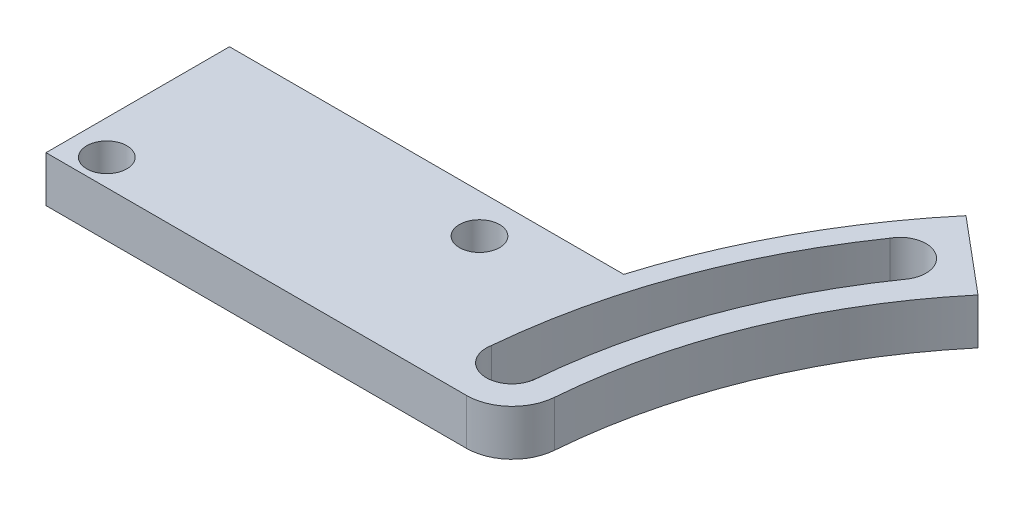
SolidWorks part; units mm, degrees
ref_plane "Front Plane" through (0, 0, 0) normal (0, 0, 1) x (1, 0, 0)
ref_plane "Top Plane" through (0, 0, 0) normal (0, 1, 0) x (1, 0, 0)
ref_plane "Right Plane" through (0, 0, 0) normal (1, 0, 0) x (0, 0, -1)
sketch "Sketch1" plane through (0, 0, 0) normal (0, 1, 0) x (1, 0, 0)
  circle A0 centre (0, 0) radius 55
  dimension "D1" = 110
extrude "Boss-Extrude1" add sketch "Sketch1" along normal blind 4
sketch "Sketch6" plane through (0, 0, 0) normal (0, 1, 0) x (1, 0, 0)
  line L0 (0, 0) -> (-87, 0) construction
  line L1 (-87, 0) -> (0, 0)
  line L2 (-87, 0) -> (-87, 16)
  line L3 (0, 0) -> (0, 16)
  line L4 (-87, 16) -> (0, 16)
  dimension "D1" = 16
  dimension "D2" = 87
extrude "Boss-Extrude2" add sketch "Sketch6" along normal blind 4
sketch "Sketch2" plane through (0, 0, 0) normal (0, 1, 0) x (1, 0, 0)
  circle A0 centre (0, 0) radius 46.5
  dimension "D1" = 93
extrude "Cut-Extrude1" cut sketch "Sketch2" along normal through all
sketch "Sketch3" plane through (0, 0, 0) normal (0, 1, 0) x (1, 0, 0)
  line L0 (0, 0) -> (-51, 0) construction
  line L1 (0, 0) -> (-50.8059, 4.4449) construction
  circle A0 centre (0, 0) radius 51 construction
  circle A1 centre (-50.8059, 4.4449) radius 2.25
  dimension "D1" = 4.5
  dimension "D3" = 102
  dimension "D2" = 5
extrude "Cut-Extrude2" cut sketch "Sketch3" along normal through all
pattern_circular "CirPattern1" count 12 over 360 about axis through (0, 0, 0) along (0, 1, 0) of "Cut-Extrude2"
sketch "Sketch4" plane through (0, 0, 0) normal (0, 1, 0) x (1, 0, 0)
  line L0 (0, 0) -> (-62.4023, 0)
  line L1 (-47.8029, 40.1114) -> (0, 0)
  arc A0 (-47.8029, 40.1114) -> (-62.4023, 0) centre (0, 0) cw
  dimension "D1" = 40
extrude "Cut-Extrude3" cut sketch "Sketch4" along normal through all
sketch "Sketch7" plane through (0, 0, 0) normal (0, 1, 0) x (1, 0, 0)
  line L0 (-87, 7.45) -> (-72.9, 7.45) construction
  line L1 (-87, 16) -> (-87, 0) construction
  line L2 (-87, 0) -> (-46.5, 0) construction
  line L3 (-84, 2.3) -> (-61.8, 2.3)
  line L4 (-84, 2.3) -> (-84, 12.6)
  line L5 (-84, 12.6) -> (-61.8, 12.6)
  line L6 (-61.8, 2.3) -> (-61.8, 12.6)
  line L7 (-72.9, 12.6) -> (-72.9, 2.3) construction
  line L8 (-84, 7.45) -> (-61.8, 7.45) construction
  circle A1 centre (-61.8, 12.6) radius 1.75
  circle A2 centre (-84, 2.3) radius 1.75
  dimension "D3" = 2.3
  dimension "D5" = 3.5
  dimension "D1" = 10.3
  dimension "D2" = 22.2
  dimension "D4" = 3
extrude "Cut-Extrude4" cut sketch "Sketch7" along normal through all contours A2 | A1
fillet "Fillet1" radius 4 1 edges at (-46.5, 2, 0)
sketch "Sketch8" plane through (0, 0, 0) normal (0, 1, 0) x (1, 0, 0)
  line L0 (0, 0) -> (-53.0556, 4.4041) construction
  line L1 (0, 0) -> (-43.6591, 30.485) construction
  line L2 (-43.6591, 30.485) -> (-39.9704, 27.9094)
  line L3 (-53.0556, 4.4041) -> (-48.5829, 4.0328)
  circle A0 centre (-50.8059, 4.4449) radius 2.25 construction
  circle A1 centre (-41.7768, 29.2524) radius 2.25 construction
  arc A2 (-53.0556, 4.4041) -> (-43.6501, 30.4788) centre (0, 0) cw
  arc A3 (-39.9704, 27.9094) -> (-48.5829, 4.0328) centre (0, 0) ccw
  dimension "D1" = 48.75
extrude "Cut-Extrude5" cut sketch "Sketch8" along normal through all contours A3 L2 A2 L3
